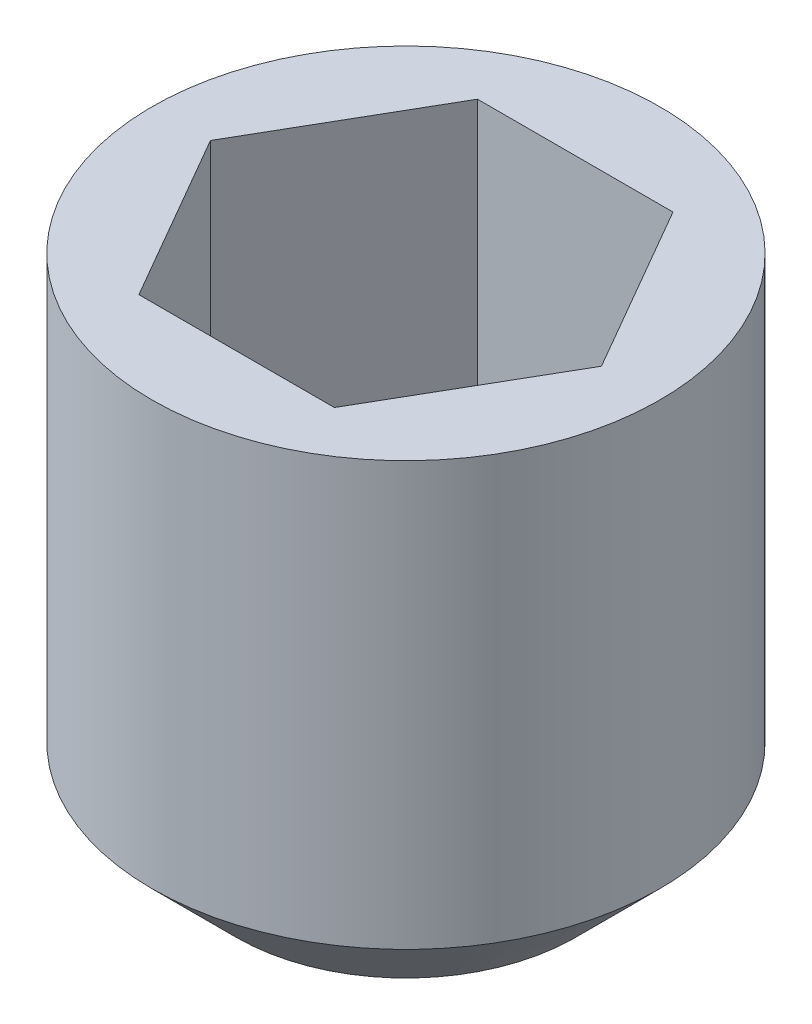
SolidWorks part; units mm, degrees
ref_plane "Front Plane" through (0, 0, 0) normal (0, 0, 1) x (1, 0, 0)
ref_plane "Top Plane" through (0, 0, 0) normal (0, 1, 0) x (1, 0, 0)
ref_plane "Right Plane" through (0, 0, 0) normal (1, 0, 0) x (0, 0, -1)
sketch "Sketch1" plane through (0, 0, 0) normal (0, 1, 0) x (1, 0, 0)
  circle A0 centre (0, 0) radius 1.5
  dimension "D1" = 3
extrude "Boss-Extrude1" add sketch "Sketch1" along normal blind 3
chamfer "Chamfer1" distance 0.5 angle 45 1 edges at (0, 0, 1.5)
sketch "Sketch2" plane through (0, 3, 0) normal (0, 1, 0) x (1, 0, 0)
  line L1 (0.5774, -1) -> (1.1547, 0)
  line L2 (1.1547, 0) -> (0.5774, 1)
  line L3 (0.5774, 1) -> (-0.5774, 1)
  line L4 (-0.5774, 1) -> (-1.1547, 0)
  line L5 (-1.1547, 0) -> (-0.5774, -1)
  line L6 (-0.5774, -1) -> (0.5774, -1)
  circle A0 centre (0, 0) radius 1 construction
  dimension "D1" = 2
extrude "Cut-Extrude1" cut sketch "Sketch2" against normal blind 1.5
